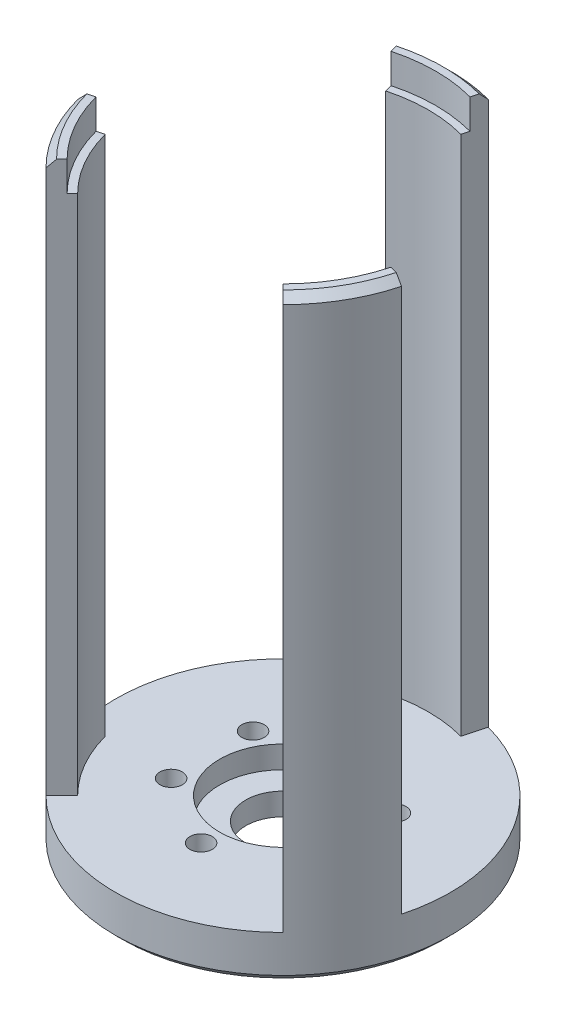
SolidWorks part; units mm, degrees
ref_plane "Front Plane" through (0, 0, 0) normal (0, 0, 1) x (1, 0, 0)
ref_plane "Top Plane" through (0, 0, 0) normal (0, 1, 0) x (1, 0, 0)
ref_plane "Right Plane" through (0, 0, 0) normal (1, 0, 0) x (0, 0, -1)
sketch "Sketch1" plane through (0, 0, 0) normal (0, 1, 0) x (1, 0, 0)
  line L0 (0, 0) -> (0, 11) construction
  line L1 (0, 0) -> (9.5263, 5.5) construction
  circle A0 centre (0, 0) radius 22.5
  circle A1 centre (0, 0) radius 11 construction
  circle A2 centre (0, 11) radius 1.5
  circle A3 centre (9.5263, 5.5) radius 1.5
  circle A4 centre (9.5263, -5.5) radius 1.5
  circle A5 centre (0, -11) radius 1.5
  circle A6 centre (-9.5263, -5.5) radius 1.5
  circle A7 centre (-9.5263, 5.5) radius 1.5
  circle A8 centre (0, 0) radius 5
  dimension "D1" = 45
  dimension "D2" = 22
  dimension "D3" = 3
  dimension "D5" = 10
  dimension "D4" = 60
extrude "Boss-Extrude1" add sketch "Sketch1" along normal blind 6
sketch "Sketch4" plane through (0, 6, 0) normal (0, 1, 0) x (1, 0, 0)
  circle A0 centre (0, 0) radius 8.5
  dimension "D1" = 17
extrude "Cut-Extrude2" cut sketch "Sketch4" against normal blind 3
sketch "Sketch6" plane through (0, 0, 0) normal (0, -1, 0) x (1, 0, 0)
  circle A0 centre (0, 11) radius 3.25
  circle A1 centre (9.5263, -5.5) radius 3.25
  circle A2 centre (-9.5263, -5.5) radius 3.25
  point P3 (0, 0)
  point P9 (0, 0)
  dimension "D1" = 6.5
  dimension "D2" = 3
extrude "Cut-Extrude3" cut sketch "Sketch6" against normal blind 2.5
sketch "Sketch2" plane through (0, 6, 0) normal (0, 1, 0) x (1, 0, 0)
  line L0 (0, 0) -> (0, 22.5) construction
  line L1 (0, 0) -> (9.5263, -5.5) construction
  line L2 (9.5263, -5.5) -> (19.4856, -11.25) construction
  line L3 (0, 0) -> (-9.5263, -5.5) construction
  line L4 (-9.5263, -5.5) -> (-19.4856, -11.25) construction
  line L5 (5.047, 18.8356) -> (5.8234, 21.7333)
  line L6 (-5.047, 18.8356) -> (-5.8234, 21.7333)
  line L7 (18.8356, -5.047) -> (21.7333, -5.8234)
  line L8 (13.7886, -13.7886) -> (15.9099, -15.9099)
  line L9 (-13.7886, -13.7886) -> (-15.9099, -15.9099)
  line L10 (-18.8356, -5.047) -> (-21.7333, -5.8234)
  circle A0 centre (0, 0) radius 22.5 construction
  arc A2 (15.9099, -15.9099) -> (21.7333, -5.8234) centre (0, 0) ccw
  arc A4 (5.8234, 21.7333) -> (-5.8234, 21.7333) centre (0, 0) ccw
  arc A5 (5.047, 18.8356) -> (-5.047, 18.8356) centre (0, 0) ccw
  arc A6 (13.7886, -13.7886) -> (18.8356, -5.047) centre (0, 0) ccw
  arc A7 (-21.7333, -5.8234) -> (-15.9099, -15.9099) centre (0, 0) ccw
  arc A8 (-18.8356, -5.047) -> (-13.7886, -13.7886) centre (0, 0) ccw
  point P26 (0, 0)
  dimension "D1" = 19.5
  dimension "D2" = 15
  dimension "D3" = 3
extrude "Boss-Extrude2" add sketch "Sketch2" along normal blind 74
sketch "Sketch7" plane through (0, 80, 0) normal (0, 1, 0) x (1, 0, 0)
  circle A0 centre (0, 0) radius 20.5
  point P5 (0, -0.5243)
  dimension "D1" = 41
extrude "Cut-Extrude4" cut sketch "Sketch7" against normal blind 4
chamfer "Chamfer2" distance 1 angle 45 4 edges at (0, 80, -22.5) (19.4856, 80, 11.25) (-19.4856, 80, 11.25) (0, 0, 22.5)
